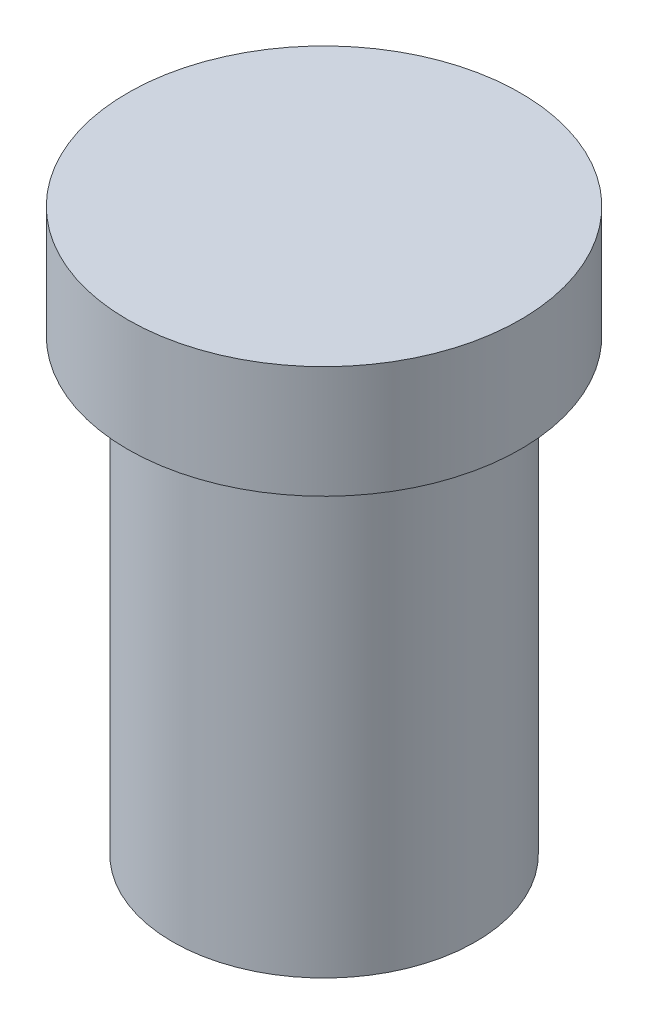
SolidWorks part; units mm, degrees
ref_plane "Front Plane" through (0, 0, 0) normal (0, 0, 1) x (1, 0, 0)
ref_plane "Top Plane" through (0, 0, 0) normal (0, 1, 0) x (1, 0, 0)
ref_plane "Right Plane" through (0, 0, 0) normal (1, 0, 0) x (0, 0, -1)
sketch "Sketch1" plane through (0, 0, 0) normal (0, 1, 0) x (1, 0, 0)
  circle A0 centre (0, 0) radius 6.75
  dimension "D1" = 13.5
extrude "Extrude1" add sketch "Sketch1" against normal blind 20
sketch "Sketch2" plane through (0, 0, 0) normal (0, 1, 0) x (1, 0, 0)
  line L0 (0, 6.75) -> (0, -6.75) construction
  line L1 (-6.75, 0) -> (6.75, 0) construction
  circle A0 centre (0, 0) radius 6.75 construction
  circle A1 centre (0, 0) radius 8.75
  point P7 (0, 0)
extrude "Extrude2" add sketch "Sketch2" along normal blind 5
